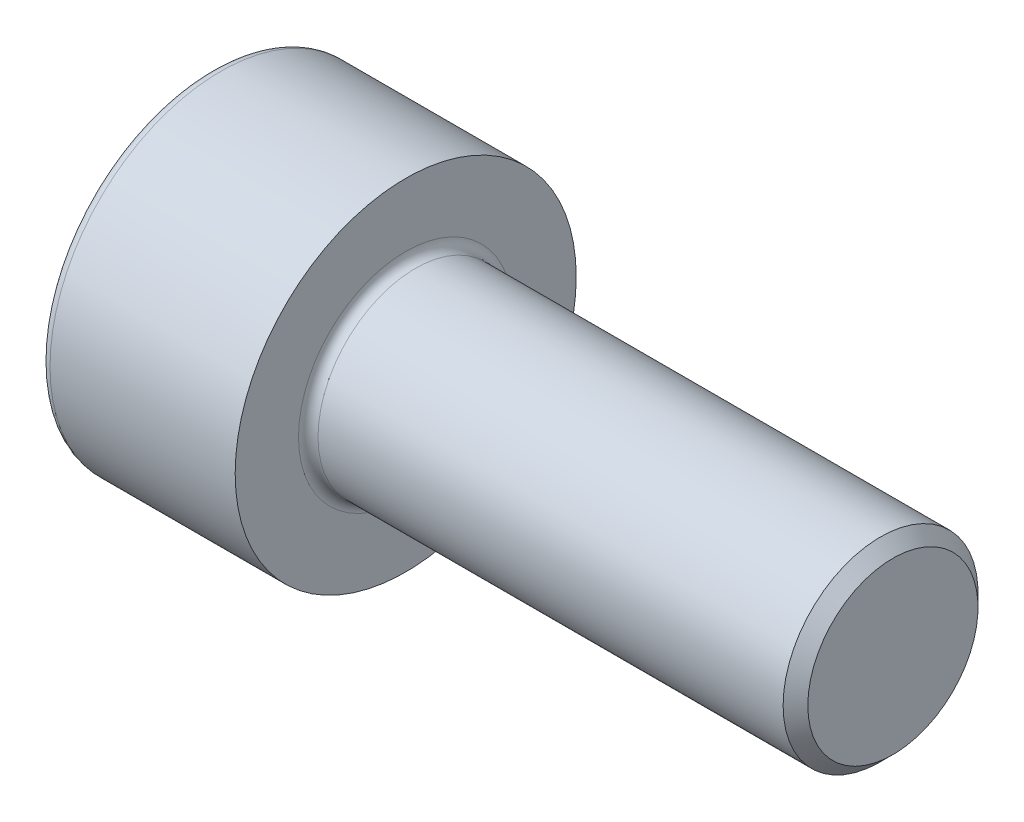
SolidWorks part; units mm, degrees
ref_plane "Front" through (0, 0, 0) normal (0, 0, 1) x (1, 0, 0)
ref_plane "Top" through (0, 0, 0) normal (0, 1, 0) x (1, 0, 0)
ref_plane "Right" through (0, 0, 0) normal (1, 0, 0) x (0, 0, -1)
sketch "Sketch1" plane through (0, 0, 0) normal (0, 0, 1) x (1, 0, 0)
  line L0 (9.7465, 2) -> (0.2, 2)
  line L1 (-4, 3.3) -> (-4, 0)
  line L2 (0, 3.5) -> (-3.8, 3.5)
  line L3 (0, 2.2) -> (0, 3.5)
  line L4 (10, 1.7465) -> (10, 0)
  line L5 (10, 1.7465) -> (9.7465, 2)
  line L6 (-4, 0) -> (0, 0) construction
  line L7 (-4, 0) -> (10, 0)
  arc A0 (-3.8, 3.5) -> (-4, 3.3) centre (-3.8, 3.3) ccw
  arc A1 (0, 2.2) -> (0.2, 2) centre (0.2, 2.2) ccw
  point P12 (0, 2.85)
  dimension "D5" = 0.2
  dimension "D1" = 4
  dimension "D2" = 7
  dimension "D3" = 135
  dimension "D4" = 0.3585
  dimension "D6" = 10
  dimension "D7" = 4
revolve "Revolve1" add sketch "Sketch1" angle 360 about L7
sketch "Sketch2" plane through (-4, 0, 0) normal (-1, 0, 0) x (0, 0, 1)
  line L7 (1.535, 0.8862) -> (0, 1.7725)
  line L8 (0, 1.7725) -> (-1.535, 0.8862)
  line L9 (-1.535, 0.8862) -> (-1.535, -0.8862)
  line L10 (-1.535, -0.8862) -> (0, -1.7725)
  line L11 (0, -1.7725) -> (1.535, -0.8862)
  line L12 (1.535, -0.8862) -> (1.535, 0.8862)
  circle A0 centre (0, 0) radius 1.535 construction
  dimension "D1" = 3.07
extrude "Cut-Extrude1" cut sketch "Sketch2" against normal blind 2
